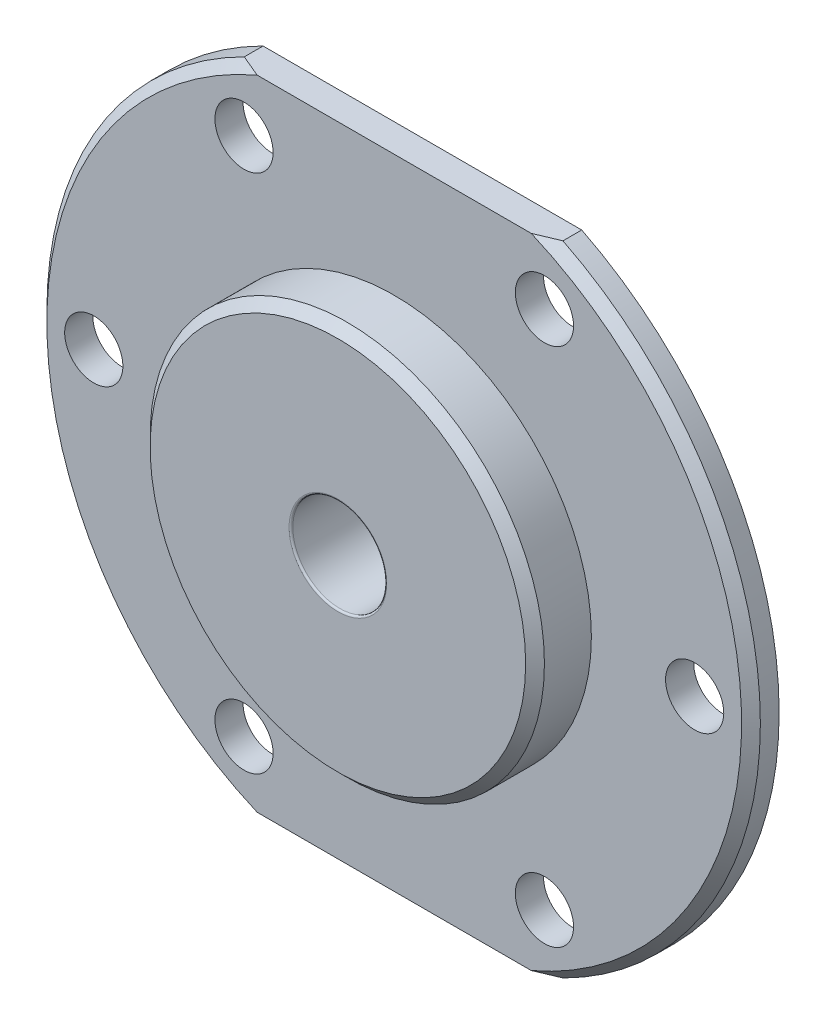
SolidWorks part; units mm, degrees
material "Stainless Steel (ferritic)"
ref_plane "Front Plane" through (0, 0, 0) normal (0, 0, 1) x (1, 0, 0)
ref_plane "Top Plane" through (0, 0, 0) normal (0, 1, 0) x (1, 0, 0)
ref_plane "Right Plane" through (0, 0, 0) normal (1, 0, 0) x (0, 0, -1)
sketch "Sketch1" plane through (0, 0, 0) normal (0, 0, 1) x (1, 0, 0)
  circle A0 centre (0, 0) radius 19
  dimension "D1" = 38
extrude "Boss-Extrude2" add sketch "Sketch1" along normal blind 1.5
sketch "Sketch2" plane through (0, 0, 1.5) normal (0, 0, 1) x (1, 0, 0)
  line L0 (-10.0946, 17) -> (12.5593, 17)
  line L1 (-8, 13.8564) -> (0, 0)
  line L2 (-11.4448, -17) -> (10.3089, -17)
  line L3 (-10.0946, 17) -> (0.5353, 23.784)
  line L4 (0.5353, 23.784) -> (12.5593, 17)
  line L5 (-11.4448, -17) -> (0, -23.4572)
  line L6 (0, -23.4572) -> (10.3089, -17)
  circle A1 centre (-8, 13.8564) radius 1.55
  circle A2 centre (8, 13.8564) radius 1.55
  circle A3 centre (16, 0) radius 1.55
  circle A4 centre (8, -13.8564) radius 1.55
  circle A5 centre (-8, -13.8564) radius 1.55
  circle A6 centre (-16, 0) radius 1.55
  point P18 (0, 0)
  dimension "D1" = 34
  dimension "D2" = 3.1
  dimension "D3" = 6
  dimension "D4" = 17
extrude "Cut-Extrude1" cut sketch "Sketch2" against normal blind 6.5
sketch "Sketch3" plane through (0, 0, 1.5) normal (0, 0, 1) x (1, 0, 0)
  circle A0 centre (0, 0) radius 10.5
  dimension "D1" = 21
extrude "Boss-Extrude3" add sketch "Sketch3" along normal blind 3
sketch "Sketch4" plane through (0, 0, 0) normal (0, 0, -1) x (-1, 0, 0)
  circle A0 centre (0, 0) radius 5
  dimension "D1" = 10
extrude "Boss-Extrude4" add sketch "Sketch4" along normal blind 5
sketch "Sketch5" plane through (0, 0, 4.5) normal (0, 0, 1) x (1, 0, 0)
  circle A0 centre (0, 0) radius 2.5
  dimension "D1" = 5
extrude "Cut-Extrude2" cut sketch "Sketch5" against normal through all
chamfer "Chamfer1" distance 0.5 angle 45 4 edges at (-5, 0, -5) (10.5, 0, 4.5) (-19, 0, 1.5) (19, 0, 1.5)
fillet "Fillet1" radius 0.1 2 edges at (2.5, 0, -5) (2.5, 0, 4.5)
